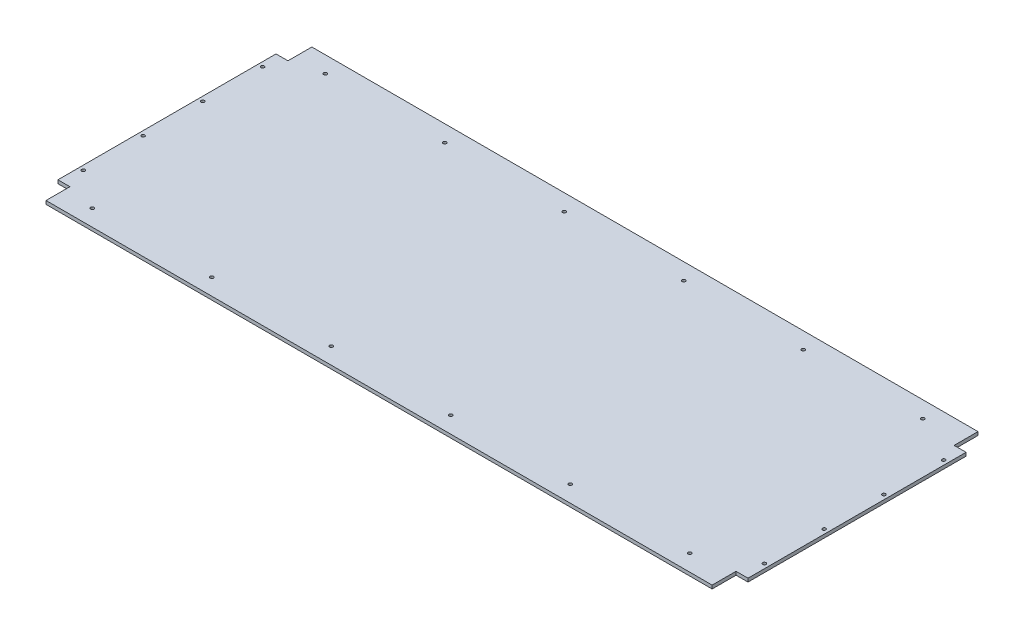
SolidWorks part; units mm, degrees
ref_plane "Front Plane" through (0, 0, 0) normal (0, 0, 1) x (1, 0, 0)
ref_plane "Top Plane" through (0, 0, 0) normal (0, 1, 0) x (1, 0, 0)
ref_plane "Right Plane" through (0, 0, 0) normal (1, 0, 0) x (0, 0, -1)
sketch "Sketch1" plane through (0, 0, 0) normal (0, 1, 0) x (1, 0, 0)
  line L0 (-577.5, 222.5) -> (577.5, -222.5) construction
  line L1 (-577.5, 222.5) -> (577.5, 222.5)
  line L2 (-577.5, 222.5) -> (-577.5, -222.5)
  line L3 (-577.5, -222.5) -> (577.5, -222.5)
  line L4 (577.5, 222.5) -> (577.5, -222.5)
  dimension "D1" = 445
  dimension "D2" = 1155
extrude "Boss-Extrude1" add sketch "Sketch1" along normal blind 5.715
sketch "Sketch2" plane through (0, 5.715, 0) normal (0, 1, 0) x (1, 0, 0)
  line L0 (-577.5, 0) -> (0, 0) construction
  line L1 (-577.5, 222.5) -> (-557.5, 222.5)
  line L2 (-577.5, 222.5) -> (-577.5, 182.5)
  line L3 (-577.5, 182.5) -> (-557.5, 182.5)
  line L4 (-557.5, 222.5) -> (-557.5, 182.5)
  line L5 (-577.5, 222.5) -> (-577.5, -222.5) construction
  line L6 (0, 0) -> (0, 222.5) construction
  line L7 (577.5, 222.5) -> (-577.5, 222.5) construction
  line L8 (-557.5, -222.5) -> (-557.5, -182.5)
  line L9 (-577.5, -182.5) -> (-557.5, -182.5)
  line L10 (-577.5, -222.5) -> (-577.5, -182.5)
  line L11 (-577.5, -222.5) -> (-557.5, -222.5)
  line L12 (577.5, -222.5) -> (557.5, -222.5)
  line L13 (577.5, -222.5) -> (577.5, -182.5)
  line L14 (577.5, -182.5) -> (557.5, -182.5)
  line L15 (557.5, -222.5) -> (557.5, -182.5)
  line L16 (557.5, 222.5) -> (557.5, 182.5)
  line L17 (577.5, 182.5) -> (557.5, 182.5)
  line L18 (577.5, 222.5) -> (577.5, 182.5)
  line L19 (577.5, 222.5) -> (557.5, 222.5)
  dimension "D1" = 40
  dimension "D2" = 20
extrude "Cut-Extrude1" cut sketch "Sketch2" against normal through all
sketch "Sketch3" plane through (0, 5.715, 0) normal (0, 1, 0) x (1, 0, 0)
  line L0 (0, 222.5) -> (0, -222.5) construction
  line L1 (557.5, 222.5) -> (-557.5, 222.5) construction
  line L2 (-557.5, -222.5) -> (557.5, -222.5) construction
  line L3 (-577.5, 0) -> (577.5, 0) construction
  line L4 (-577.5, 182.5) -> (-577.5, -182.5) construction
  line L5 (577.5, -182.5) -> (577.5, 182.5) construction
  line L6 (-557.5, 182.5) -> (-557.5, 222.5) construction
  line L7 (-577.5, 182.5) -> (-557.5, 182.5) construction
  line L8 (-507.5, 195) -> (-307.5, 195) construction
  line L9 (-570, 152.5) -> (-570, 52.5) construction
  circle A0 centre (-507.5, 195) radius 2.75
  circle A1 centre (-570, 152.5) radius 2.75
  circle A2 centre (-307.5, 195) radius 2.75
  circle A3 centre (-107.5, 195) radius 2.75
  circle A4 centre (92.5, 195) radius 2.75
  circle A5 centre (292.5, 195) radius 2.75
  circle A6 centre (492.5, 195) radius 2.75
  circle A7 centre (-570, 52.5) radius 2.75
  circle A8 centre (-570, -47.5) radius 2.75
  circle A9 centre (-570, -147.5) radius 2.75
  circle A10 centre (492.5, -195) radius 2.75
  circle A11 centre (292.5, -195) radius 2.75
  circle A12 centre (92.5, -195) radius 2.75
  circle A13 centre (-107.5, -195) radius 2.75
  circle A14 centre (-307.5, -195) radius 2.75
  circle A15 centre (-507.5, -195) radius 2.75
  circle A16 centre (570, -147.5) radius 2.75
  circle A17 centre (570, -47.5) radius 2.75
  circle A18 centre (570, 52.5) radius 2.75
  circle A19 centre (570, 152.5) radius 2.75
  dimension "D1" = 390
  dimension "D3" = 5.5
  dimension "D5" = 30
  dimension "D2" = 50
  dimension "D4" = 1140
  dimension "D7" = 200
  dimension "D9" = 100
  dimension "D6" = 6
  dimension "D8" = 4
extrude "Cut-Extrude2" cut sketch "Sketch3" against normal through all
